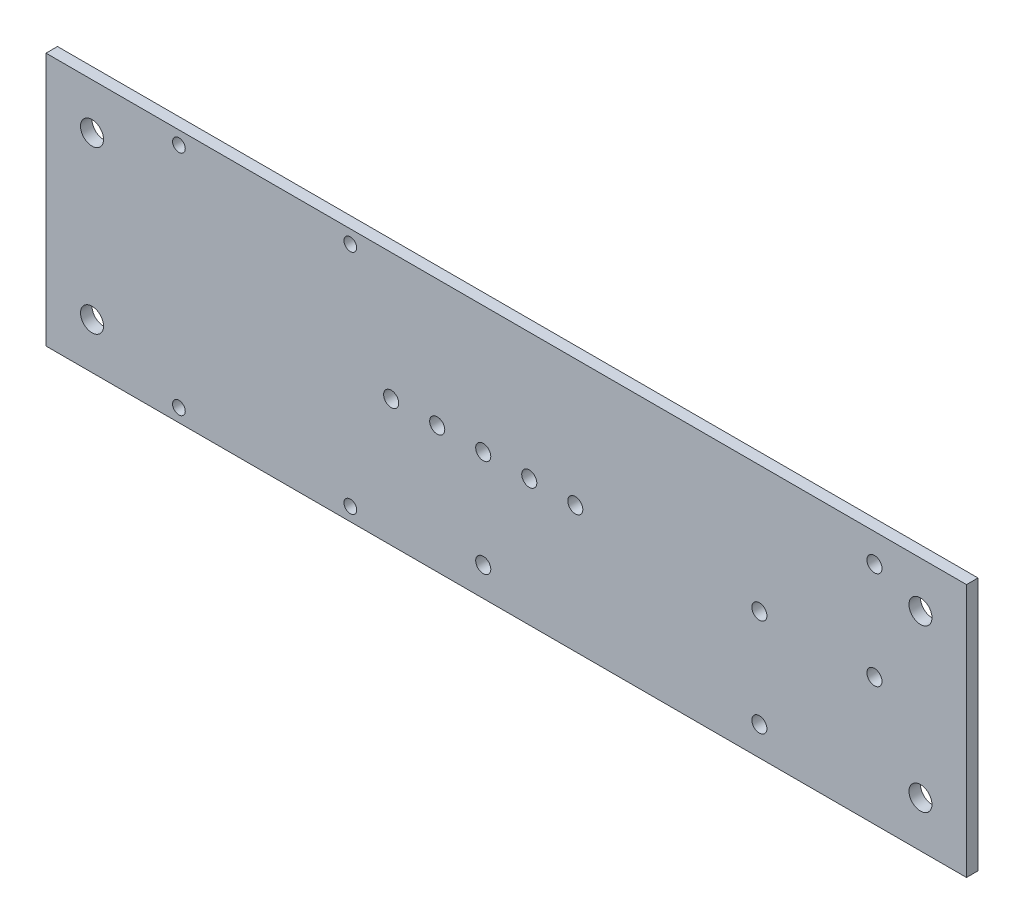
SolidWorks part; units mm, degrees
ref_plane "Front Plane" through (0, 0, 0) normal (0, 0, 1) x (1, 0, 0)
ref_plane "Top Plane" through (0, 0, 0) normal (0, 1, 0) x (1, 0, 0)
ref_plane "Right Plane" through (0, 0, 0) normal (1, 0, 0) x (0, 0, -1)
sketch "Sketch1" plane through (0, 0, 0) normal (0, 0, 1) x (1, 0, 0)
  line L1 (0, 0) -> (254, 0)
  line L2 (0, 0) -> (0, 70)
  line L3 (0, 70) -> (254, 70)
  line L4 (254, 0) -> (254, 70)
  dimension "D1" = 70
  dimension "D2" = 254
extrude "Boss-Extrude1" add sketch "Sketch1" along normal blind 3.175
hole_wizard "#8-32 Tapped Hole1" positions "Sketch3" profile "Sketch2" tap size "#8-32" standard "ANSI Inch" end condition through all
sketch "Sketch3" plane through (0, 0, 3.175) normal (0, 0, 1) x (1, 0, 0)
  line L0 (228.6, 62.1874) -> (254, 62.1874) construction
  line L1 (254, 0) -> (254, 70) construction
  line L2 (196.85, 35) -> (228.6, 62.1874) construction
  line L4 (196.85, 35) -> (254, 35) construction
  line L6 (254, 70) -> (254, 62.1874) construction
  line L9 (254, 35) -> (254, 0) construction
  line L10 (95.25, 35) -> (120.65, 35) construction
  line L11 (120.65, 35) -> (146.05, 35) construction
  point P4 (228.6, 62.1874)
  point P25 (196.85, 35)
  point P99 (95.25, 35)
  point P101 (120.65, 35)
  point P103 (146.05, 35)
  point P114 (133.35, 35)
  point P116 (107.95, 35)
  dimension "D1" = 31.75
  dimension "D2" = 27.1874
  dimension "D3" = 25.4
  dimension "D4" = 25.4
  dimension "D5" = 76.2
sketch "Sketch2" plane through (228.6, 62.1874, 3.175) normal (1, 0, 0) x (0, -1, 0)
  line L0 (0, 0) -> (0, 3.175)
  line L1 (0, 3.175) -> (2.0828, 3.175)
  line L2 (2.0828, 3.175) -> (2.0828, 0)
  line L5 (2.0828, 0) -> (0, 0)
  line L11 (0, -6.35) -> (0, 107.95) construction
  dimension "Thread Major Dia." = 4.1656
  dimension "Thru Tap Drill Depth" = 3.175
hole_wizard "#6-32 Tapped Hole1" positions "Sketch6" profile "Sketch4" tap size "#6-32" standard "ANSI Inch" end condition through all
sketch "Sketch6" plane through (0, 0, 3.175) normal (0, 0, 1) x (1, 0, 0)
  point P0 (36.6736, 66.3681)
  point P3 (83.9726, 66.3249)
  point P6 (83.9726, 3.6751)
  point P9 (36.6736, 3.6319)
sketch "Sketch4" plane through (36.6736, 66.3681, 3.175) normal (1, 0, 0) x (0, -1, 0)
  line L0 (0, 0) -> (0, 3.175)
  line L1 (0, 3.175) -> (1.7526, 3.175)
  line L2 (1.7526, 3.175) -> (1.7526, 0)
  line L5 (1.7526, 0) -> (0, 0)
  line L11 (0, -6.35) -> (0, 107.95) construction
  dimension "Thread Major Dia." = 3.5052
  dimension "Thru Tap Drill Depth" = 3.175
hole_wizard "1/4-20 Tapped Hole1" positions "Sketch9" profile "Sketch7" tap size "1/4-20" standard "ANSI Inch" end condition through all
sketch "Sketch9" plane through (0, 0, 3.175) normal (0, 0, 1) x (1, 0, 0)
  line L0 (12.7, 70) -> (12.7, 57.3) construction
  line L1 (254, 70) -> (0, 70) construction
  line L2 (12.7, 57.3) -> (12.7, 12.7) construction
  line L3 (12.7, 12.7) -> (12.7, 0) construction
  line L4 (0, 0) -> (254, 0) construction
  line L10 (0, 57.3) -> (12.7, 57.3) construction
  line L11 (0, 70) -> (0, 0) construction
  line L12 (12.7, 57.3) -> (241.3, 57.3) construction
  line L13 (241.3, 57.3) -> (254, 57.3) construction
  line L14 (254, 0) -> (254, 70) construction
  point P2 (12.7, 57.3)
  point P4 (241.3, 12.7)
  point P6 (241.3, 57.3)
  point P12 (12.7, 12.7)
  dimension "D1" = 12.7
sketch "Sketch7" plane through (12.7, 57.3, 3.175) normal (1, 0, 0) x (0, -1, 0)
  line L0 (0, 0) -> (0, 3.175)
  line L1 (0, 3.175) -> (3.175, 3.175)
  line L2 (3.175, 3.175) -> (3.175, 0)
  line L5 (3.175, 0) -> (0, 0)
  line L11 (0, -6.35) -> (0, 107.95) construction
  dimension "Thread Major Dia." = 6.35
  dimension "Thru Tap Drill Depth" = 3.175
hole_wizard "#8-32 Tapped Hole2" positions "Sketch11" profile "Sketch10" tap size "#8-32" standard "ANSI Inch" end condition through all
sketch "Sketch11" plane through (0, 0, 3.175) normal (0, 0, 1) x (1, 0, 0)
  point P0 (228.6, 35.1999)
  point P3 (196.85, 8.0125)
  point P6 (120.65, 8.0125)
sketch "Sketch10" plane through (228.6, 35.1999, 3.175) normal (1, 0, 0) x (0, -1, 0)
  line L0 (0, 0) -> (0, 3.175)
  line L1 (0, 3.175) -> (2.0828, 3.175)
  line L2 (2.0828, 3.175) -> (2.0828, 0)
  line L5 (2.0828, 0) -> (0, 0)
  line L11 (0, -6.35) -> (0, 107.95) construction
  dimension "Thread Major Dia." = 4.1656
  dimension "Thru Tap Drill Depth" = 3.175
